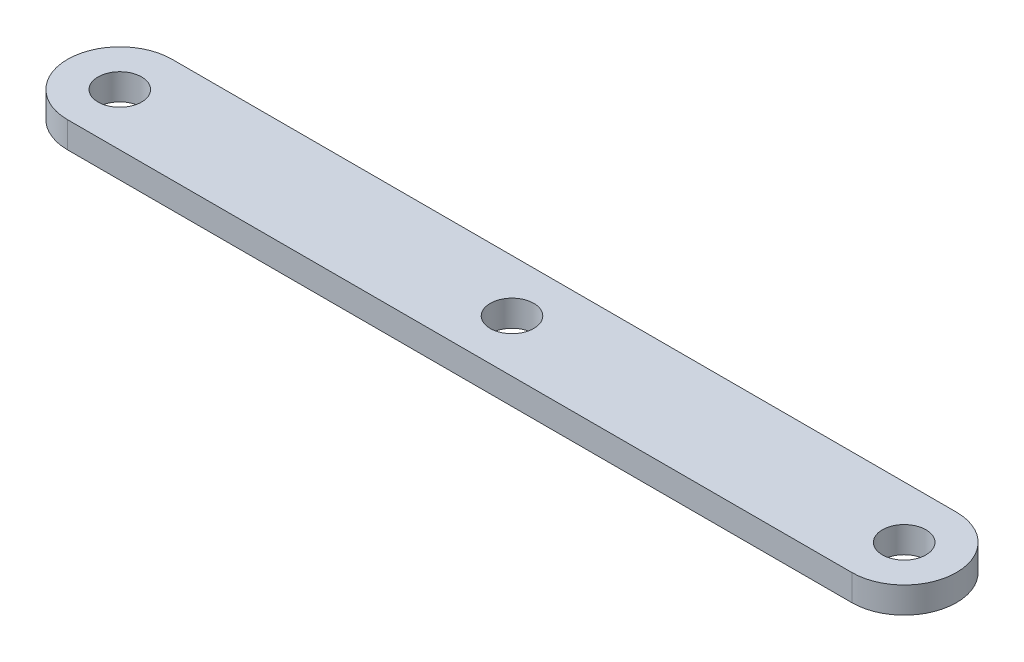
SolidWorks part; units mm, degrees
ref_plane "前基準面" through (0, 0, 0) normal (0, 0, 1) x (1, 0, 0)
ref_plane "上基準面" through (0, 0, 0) normal (0, 1, 0) x (1, 0, 0)
ref_plane "右基準面" through (0, 0, 0) normal (1, 0, 0) x (0, 0, -1)
sketch "草圖1" plane through (0, 0, 0) normal (0, 1, 0) x (1, 0, 0)
  line L0 (-45, 0) -> (45, 0) construction
  line L1 (-45, 6) -> (45, 6)
  line L2 (-45, -6) -> (45, -6)
  arc A0 (-45, 6) -> (-45, -6) centre (-45, 0) ccw
  arc A1 (45, -6) -> (45, 6) centre (45, 0) ccw
  point P3 (0, 0)
  dimension "D2" = 6
  dimension "D1" = 90
  dimension "D3" = 45
extrude "填料-伸長1" add sketch "草圖1" along normal blind 3
sketch "草圖2" plane through (0, 3, 0) normal (0, 1, 0) x (1, 0, 0)
  circle A0 centre (-45, 0) radius 2.5
  circle A1 centre (45, 0) radius 2.5
  circle A2 centre (0, 0) radius 2.5
  dimension "D1" = 5
  dimension "D2" = 5
  dimension "D3" = 5
extrude "除料-伸長1" cut sketch "草圖2" against normal up to next
